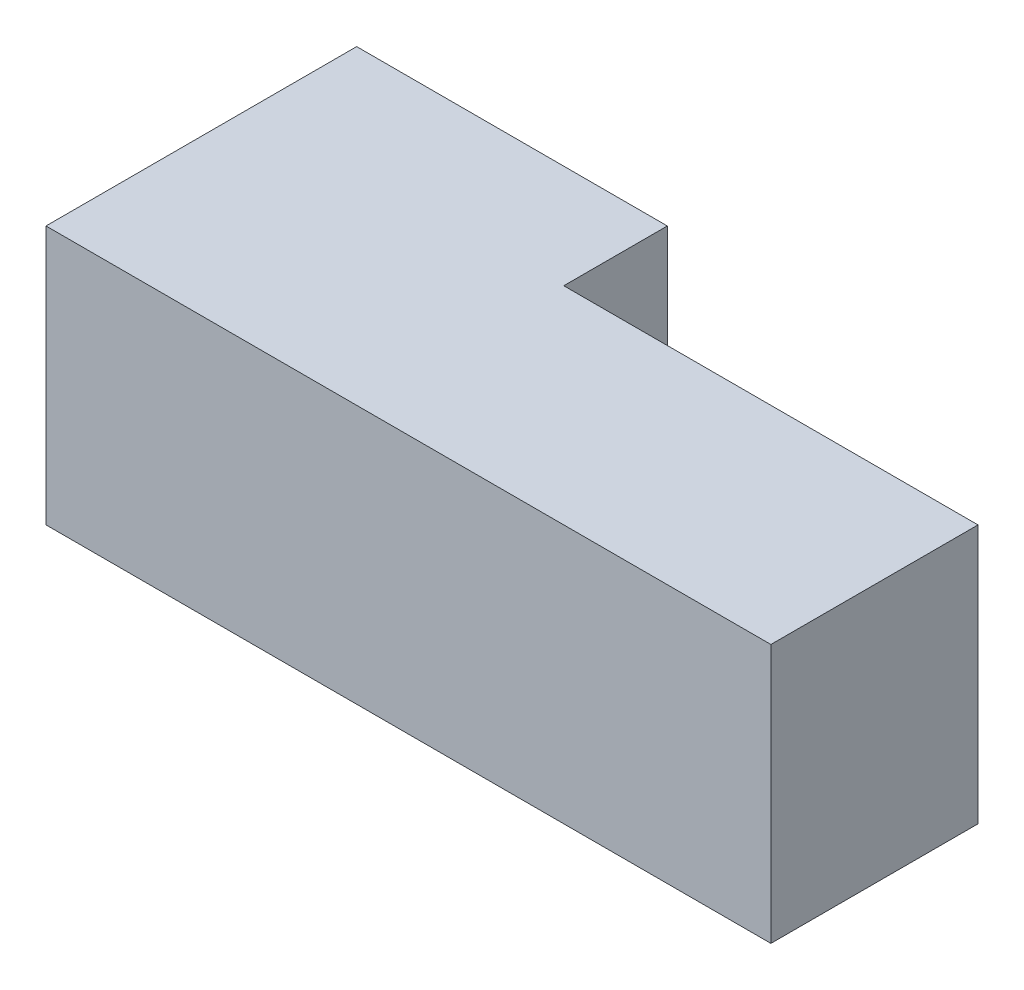
SolidWorks part; units mm, degrees
ref_plane "Front Plane" through (0, 0, 0) normal (0, 0, 1) x (1, 0, 0)
ref_plane "Top Plane" through (0, 0, 0) normal (0, 1, 0) x (1, 0, 0)
ref_plane "Right Plane" through (0, 0, 0) normal (1, 0, 0) x (0, 0, -1)
sketch "Sketch1" plane through (0, 0, 0) normal (0, 1, 0) x (1, 0, 0)
  line L0 (30, 30) -> (30, 20)
  line L1 (0, 0) -> (70, 0)
  line L2 (0, 0) -> (0, 30)
  line L3 (0, 30) -> (30, 30)
  line L4 (70, 0) -> (70, 20)
  line L5 (30, 20) -> (70, 20)
  dimension "D1" = 30
  dimension "D2" = 20
  dimension "D3" = 30
  dimension "D4" = 70
extrude "Boss-Extrude1" add sketch "Sketch1" along normal blind 25
